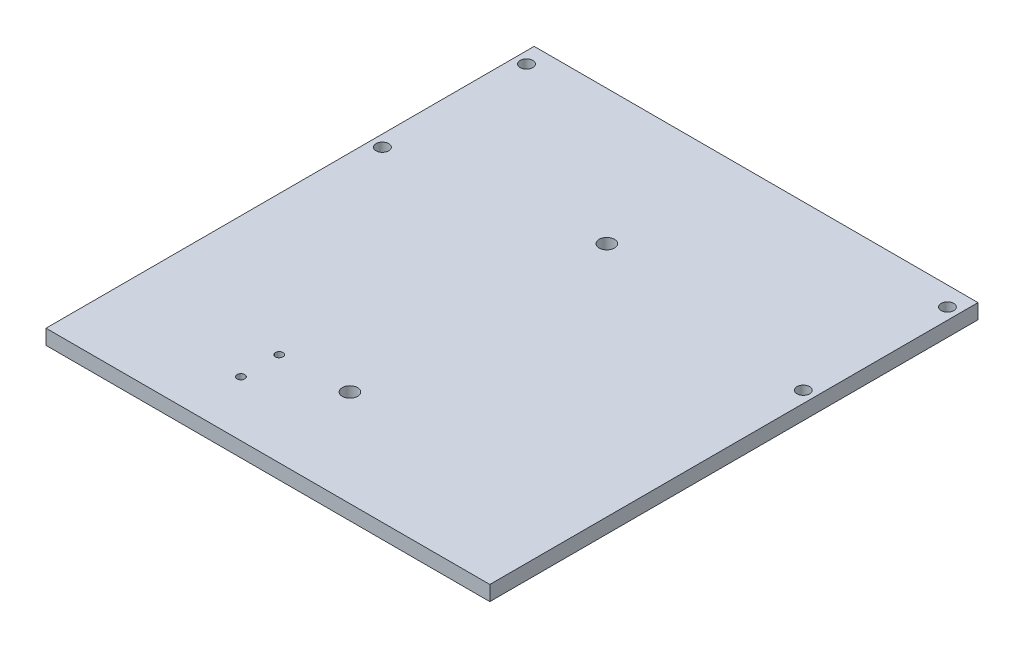
SolidWorks part; units mm, degrees
ref_plane "Front Plane" through (0, 0, 0) normal (0, 0, 1) x (1, 0, 0)
ref_plane "Top Plane" through (0, 0, 0) normal (0, 1, 0) x (1, 0, 0)
ref_plane "Right Plane" through (0, 0, 0) normal (1, 0, 0) x (0, 0, -1)
sketch "Sketch1" plane through (0, 0, 0) normal (0, 1, 0) x (1, 0, 0)
  line L1 (0, 0) -> (116.1, 0)
  line L2 (0, 0) -> (0, 47.7)
  line L3 (0, 47.7) -> (116.1, 47.7)
  line L4 (116.1, 0) -> (116.1, 47.7)
  dimension "D1" = 116.1
  dimension "D2" = 47.7
extrude "Boss-Extrude1" add sketch "Sketch1" along normal blind 3.9
sketch "Sketch4" plane through (0, 3.9, 0) normal (0, 1, 0) x (1, 0, 0)
  line L0 (0, 47.7) -> (0, 0) construction
  line L1 (116.1, 47.7) -> (0, 47.7) construction
  circle A0 centre (3, 42.7) radius 1.65
  dimension "D1" = 3.3
  dimension "D2" = 3
  dimension "D3" = 5
extrude "Cut-Extrude3" cut sketch "Sketch4" against normal through all
sketch "Sketch5" plane through (0, 3.9, 0) normal (0, 1, 0) x (1, 0, 0)
  line L0 (0, 0) -> (116.1, 0) construction
  line L1 (0, 47.7) -> (0, 0) construction
  circle A0 centre (3, 5) radius 1.65
  dimension "D3" = 3.3
  dimension "D1" = 5
  dimension "D2" = 3
extrude "Cut-Extrude4" cut sketch "Sketch5" against normal through all
ref_plane "Plane1" through (58.05, 0, 0) normal (-1, 0, 0) x (0, 0, 1)
mirror "Mirror1" about plane through (58.05, 0, 0) normal (-1, 0, 0) of "Cut-Extrude4", "Cut-Extrude3"
sketch "Sketch7" plane through (0, 0, 0) normal (0, 0, 1) x (1, 0, 0)
  line L1 (0, 3.9) -> (116.1, 3.9)
  line L2 (0, 3.9) -> (0, 0)
  line L3 (0, 0) -> (116.1, 0)
  line L4 (116.1, 3.9) -> (116.1, 0)
extrude "Boss-Extrude2" add sketch "Sketch7" along normal blind 80
sketch "Sketch8" plane through (0, 3.9, 0) normal (0, 1, 0) x (1, 0, 0)
  line L0 (0, 47.7) -> (0, -80) construction
  line L1 (116.1, -80) -> (0, -80) construction
  circle A0 centre (54.2, -54.7) radius 2
  circle A1 centre (54.2, 12.5) radius 2
  dimension "D3" = 4
  dimension "D6" = 4
  dimension "D1" = 54.2
  dimension "D2" = 25.3
  dimension "D4" = 54.2
  dimension "D5" = 67.2
extrude "Cut-Extrude5" cut sketch "Sketch8" against normal through all
sketch "Sketch9" plane through (0, 3.9, 0) normal (0, 1, 0) x (1, 0, 0)
  line L0 (116.1, -80) -> (0, -80) construction
  line L1 (0, 47.7) -> (0, -80) construction
  circle A0 centre (36.5, -65.5) radius 1
  circle A1 centre (36.5, -55.5) radius 1
  dimension "D5" = 2
  dimension "D6" = 2
  dimension "D1" = 14.5
  dimension "D2" = 36.5
  dimension "D3" = 36.5
  dimension "D4" = 24.5
extrude "Cut-Extrude6" cut sketch "Sketch9" against normal through all
